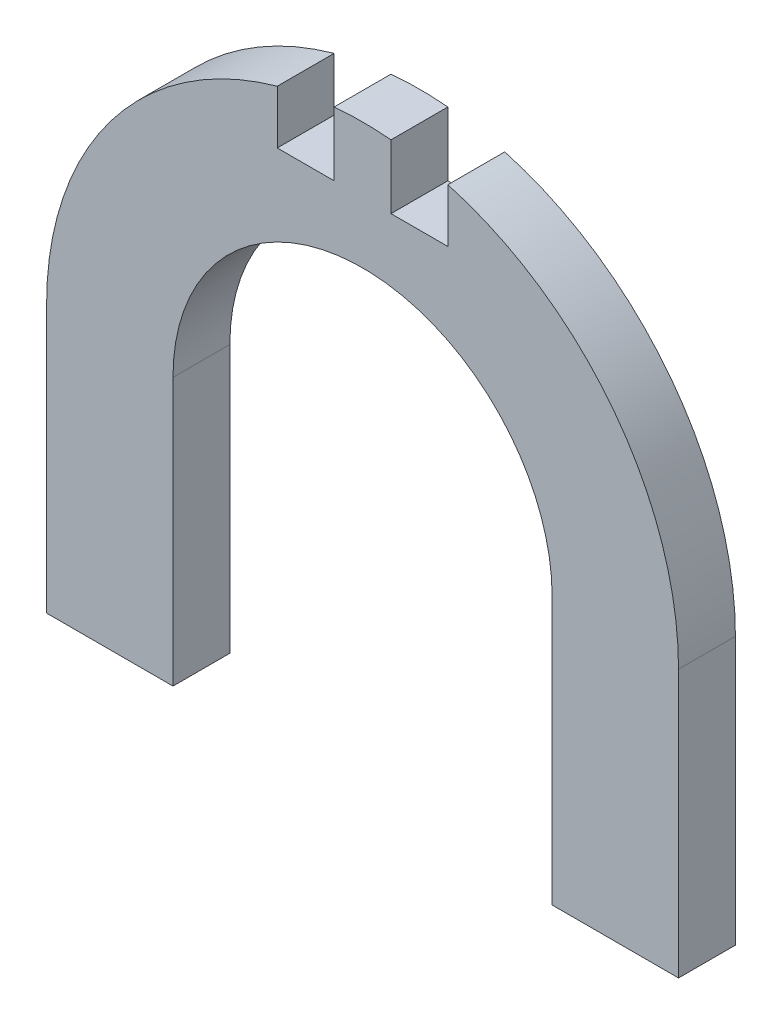
SolidWorks part; units mm, degrees
ref_plane "Спереди" through (0, 0, 0) normal (0, 0, 1) x (1, 0, 0)
ref_plane "Сверху" through (0, 0, 0) normal (0, 1, 0) x (1, 0, 0)
ref_plane "Справа" through (0, 0, 0) normal (1, 0, 0) x (0, 0, -1)
sketch "Sketch1" plane through (0, 0, 0) normal (0, 0, 1) x (1, 0, 0)
  line L0 (0, -2578.3526) -> (0, 126339.278) construction
  line L1 (60, 60) -> (60, 100.6465)
  line L2 (60, 60) -> (100, 60)
  line L3 (100, 60) -> (100, 100.6465)
  line L4 (-100, 60) -> (-100, 100.6465)
  line L5 (9, 180) -> (27, 180) construction
  line L6 (9, 180) -> (9, 160) construction
  line L7 (9, 160) -> (27, 160) construction
  line L8 (27, 180) -> (27, 160) construction
  line L9 (9, 180) -> (27, 160) construction
  line L10 (9, 160) -> (27, 180) construction
  line L11 (90, 40) -> (72, 40) construction
  line L12 (90, 40) -> (90, 80) construction
  line L13 (90, 80) -> (72, 80) construction
  line L14 (72, 40) -> (72, 80) construction
  line L15 (90, 40) -> (72, 80) construction
  line L16 (90, 80) -> (72, 40) construction
  line L17 (-60, 60) -> (-100, 60)
  line L18 (-60, 60) -> (-60, 100.6465)
  arc A0 (60, 100.6465) -> (-60, 100.6465) centre (0, 100.6465) ccw
  arc A1 (-100, 100.6465) -> (100, 100.6465) centre (0, 100.6465) cw
  point P9 (18, 170)
  point P18 (81, 60)
  dimension "D11" = 60
  dimension "D12" = 60
  dimension "D1" = 18
  dimension "D2" = 9
  dimension "D3" = 160
  dimension "D4" = 20
  dimension "D5" = 60
  dimension "D6" = 40
  dimension "D7" = 18
  dimension "D8" = 10
  dimension "D9" = 40
extrude "Boss-Extrude1" add sketch "Sketch1" along normal blind 18
sketch "Sketch2" plane through (0, 0, 18) normal (0, 0, 1) x (1, 0, 0)
  line L0 (0, -799.3535) -> (0, 799.3535) construction
  line L1 (9, 180) -> (27, 180)
  line L2 (9, 180) -> (9, 226.6701)
  line L3 (9, 226.6701) -> (27, 226.6701)
  line L4 (27, 180) -> (27, 226.6701)
  line L9 (-9, 226.6701) -> (-27, 226.6701)
  line L10 (-27, 180) -> (-27, 226.6701)
  line L11 (-9, 180) -> (-27, 180)
  line L12 (-9, 180) -> (-9, 226.6701)
  arc A0 (100, 100.6465) -> (-100, 100.6465) centre (0, 100.6465) ccw construction
  point P4 (0, 0)
  point P14 (0, 200.6465)
  dimension "D1" = 18
  dimension "D2" = 18
  dimension "D3" = 180
extrude "Cut-Extrude1" cut sketch "Sketch2" against normal through all
sketch "Sketch3" plane through (0, 60, 0) normal (0, -1, 0) x (1, 0, 0)
  line L1 (-100, 18) -> (-60, 18)
  line L2 (-100, 18) -> (-100, 0)
  line L3 (-100, 0) -> (-60, 0)
  line L4 (-60, 18) -> (-60, 0)
  line L5 (60, 18) -> (100, 18)
  line L6 (60, 18) -> (60, 0)
  line L7 (60, 0) -> (100, 0)
  line L8 (100, 18) -> (100, 0)
extrude "Boss-Extrude2" add sketch "Sketch3" along normal blind 44
